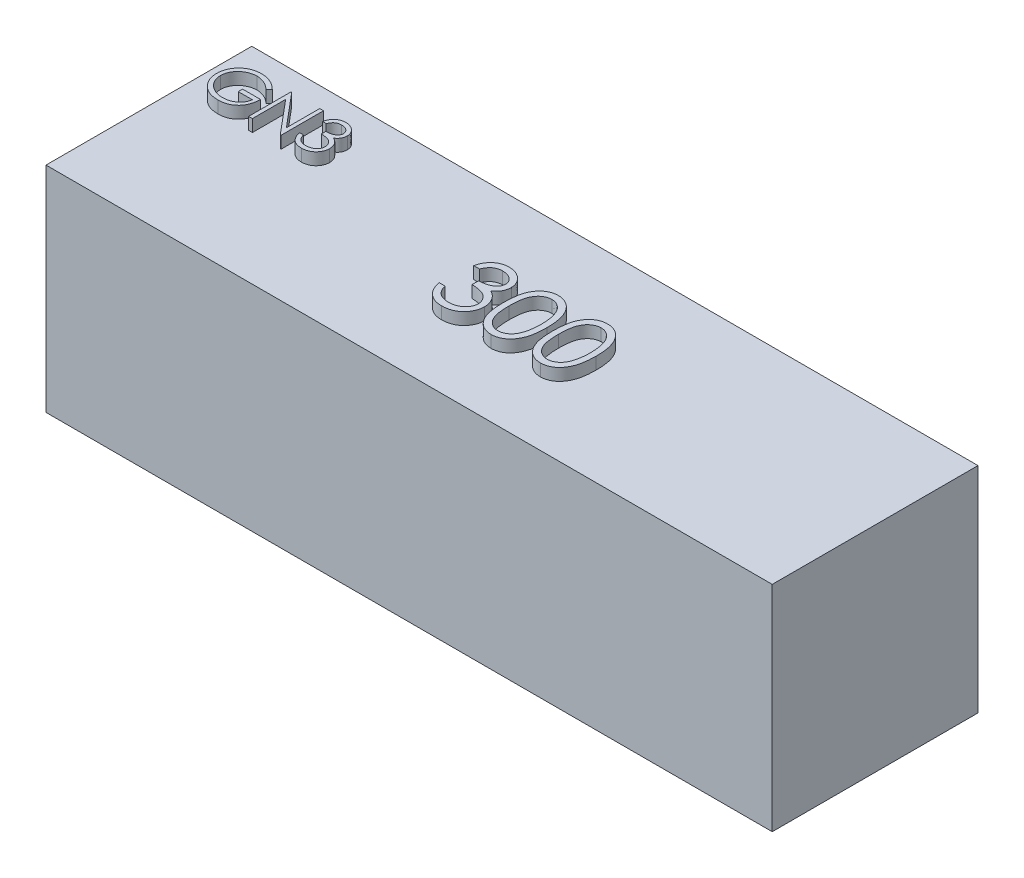
SolidWorks part; units mm, degrees
ref_plane "Front Plane" through (0, 0, 0) normal (0, 0, 1) x (1, 0, 0)
ref_plane "Top Plane" through (0, 0, 0) normal (0, 1, 0) x (1, 0, 0)
ref_plane "Right Plane" through (0, 0, 0) normal (1, 0, 0) x (0, 0, -1)
sketch "Sketch5" plane through (0, 0, 0) normal (0, 0, 1) x (1, 0, 0)
  line L1 (0, 0) -> (60, 0)
  line L2 (0, 0) -> (0, 17.7)
  line L3 (0, 17.7) -> (60, 17.7)
  line L4 (60, 0) -> (60, 17.7)
  dimension "D1" = 60
  dimension "D2" = 17.7
extrude "Boss-Extrude2" add sketch "Sketch5" along normal blind 17
sketch "Sketch6" plane through (0, 17.7, 0) normal (0, 1, 0) x (1, 0, 0)
  text T0 "GN3"
  text T1 "300" font "Century Gothic" height in points 20
extrude "Boss-Extrude3" add sketch "Sketch6" along normal blind 1
